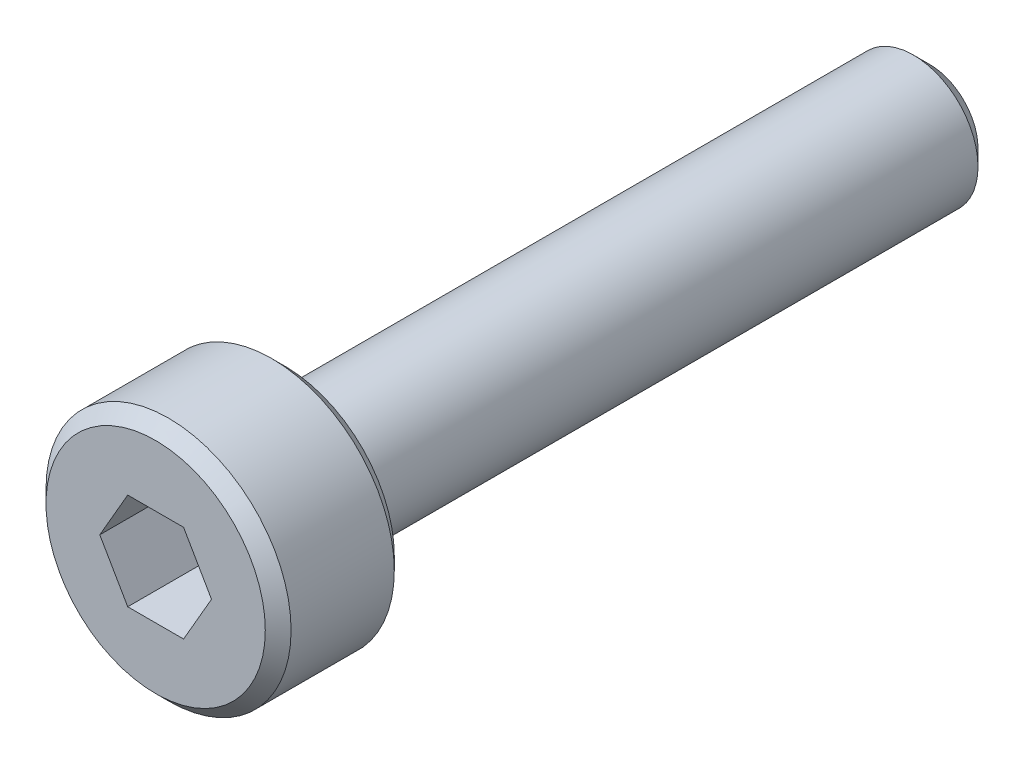
SolidWorks part; units mm, degrees
ref_plane "Спереди" through (0, 0, 0) normal (0, 0, 1) x (1, 0, 0)
ref_plane "Сверху" through (0, 0, 0) normal (0, 1, 0) x (1, 0, 0)
ref_plane "Справа" through (0, 0, 0) normal (1, 0, 0) x (0, 0, -1)
sketch "Эскиз1" plane through (0, 0, 0) normal (0, 1, 0) x (1, 0, 0)
  line L0 (0, 0) -> (0, 14.7638) construction
  line L1 (0, 0) -> (1.7, 0)
  line L2 (1.9, 0.2) -> (1.9, 1.8)
  line L3 (1.7, 2) -> (1, 2)
  line L4 (1, 2) -> (1, 11.75)
  line L5 (1, 11.75) -> (0.75, 12)
  line L6 (0.75, 12) -> (0, 12)
  line L7 (0, 12) -> (0, 0)
  line L8 (1.9, 1.8) -> (1.7, 2)
  line L9 (1.7, 0) -> (1.9, 0.2)
  point P4 (1.9, 0)
  point P5 (1.9, 2)
  dimension "D1" = 45
  dimension "D2" = 0.25
  dimension "D3" = 2
  dimension "D4" = 3.8
  dimension "D5" = 2
  dimension "D6" = 10
  dimension "D7" = 0.2
  dimension "D8" = 45
  dimension "D9" = 0.2
  dimension "D10" = 45
revolve "Повернуть1" add sketch "Эскиз1" angle 360 about L0
sketch "Эскиз2" plane through (0, 0, 0) normal (0, 0, 1) x (1, 0, 0)
  line L1 (0.866, 0) -> (0.433, 0.75)
  line L2 (0.433, 0.75) -> (-0.433, 0.75)
  line L3 (-0.433, 0.75) -> (-0.866, 0)
  line L4 (-0.866, 0) -> (-0.433, -0.75)
  line L5 (-0.433, -0.75) -> (0.433, -0.75)
  line L6 (0.433, -0.75) -> (0.866, 0)
  circle A0 centre (0, 0) radius 0.75 construction
  dimension "D1" = 1.5
extrude "Вырез-Вытянуть1" cut sketch "Эскиз2" against normal blind 1.8
